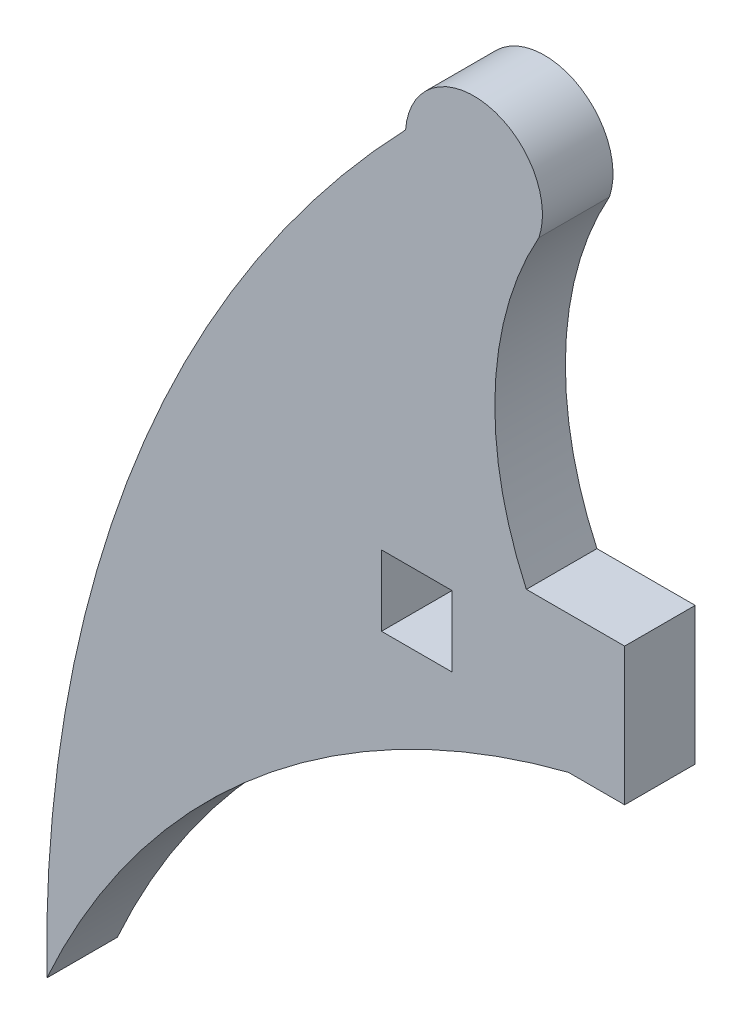
SolidWorks part; units mm, degrees
ref_plane "Front Plane" through (0, 0, 0) normal (0, 0, 1) x (1, 0, 0)
ref_plane "Top Plane" through (0, 0, 0) normal (0, 1, 0) x (1, 0, 0)
ref_plane "Right Plane" through (0, 0, 0) normal (1, 0, 0) x (0, 0, -1)
sketch "Sketch1" plane through (0, 0, 0) normal (0, 0, 1) x (1, 0, 0)
  line L0 (-22.2257, -1.524) -> (-22.2257, -2.1451)
  line L1 (-22.2257, -1.524) -> (-22.2257, -2.3495) construction
  line L2 (-22.2257, -2.1451) -> (-23.443, -2.1451)
  line L3 (-24.3487, 0.8255) -> (-22.2257, 0.8255)
  line L4 (-22.2257, 0.8255) -> (-22.2257, -1.524)
  line L6 (-25.9548, -1.524) -> (-27.4788, -1.524)
  line L7 (-25.9548, -1.524) -> (-25.9548, 0)
  line L8 (-25.9548, 0) -> (-27.4788, 0)
  line L9 (-27.4788, -1.524) -> (-27.4788, 0)
  arc A0 (-23.443, -2.1451) -> (-34.7097, -11.6265) centre (-19.2661, -18.5432) ccw
  arc A1 (-34.7097, -11.6265) -> (-26.9585, 8.118) centre (-6.8977, -11.151) cw
  arc A2 (-26.9585, 8.118) -> (-24.078, 7.5419) centre (-25.4821, 8.0107) cw
  arc A3 (-24.078, 7.5419) -> (-24.3487, 0.8255) centre (-17.6689, 3.9199) ccw
extrude "Boss-Extrude1" add sketch "Sketch1" along normal blind 1.524
